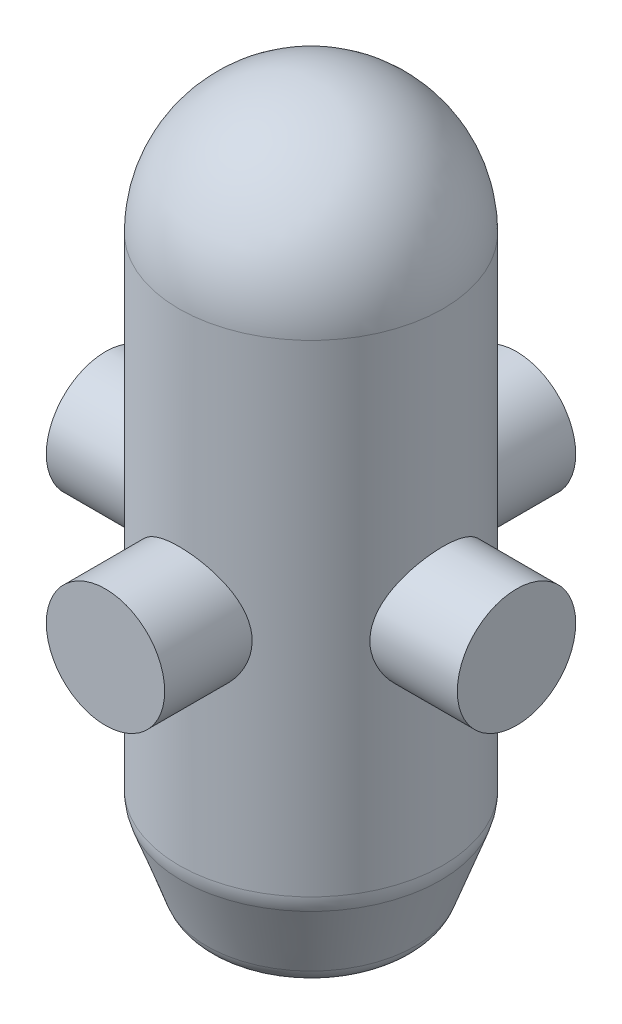
SolidWorks part; units mm, degrees
material "Ceramic Porcelain"
ref_plane "Front" through (0, 0, 0) normal (0, 0, 1) x (1, 0, 0)
ref_plane "Top"
ref_plane "Right" through (0, 0, 0) normal (1, 0, 0) x (0, 0, -1)
sketch "Sketch1" plane through (0, 0, 0) normal (0, 0, 1) x (1, 0, 0)
  line L0 (0, 0) -> (6.2866, 0)
  line L1 (6.2866, 0) -> (6.2866, -23.3)
  line L2 (6.2866, -23.3) -> (4.6488, -27.8)
  line L3 (4.6488, -27.8) -> (0, -27.8)
  line L4 (0, -27.8) -> (0, 0)
  dimension "D1" = 6.2866
  dimension "D2" = 27.8
  dimension "D3" = 20
  dimension "D4" = 4.5
revolve "Revolve1" add sketch "Sketch1" angle 360 about L4
fillet "Fillet1" radius 2 1 edges at (0, -23.3, -6.2866)
fillet "Fillet2" radius 1.3 1 edges at (0, -27.8, -4.6488)
sketch "Sketch2" plane through (0, 0, 0) normal (1, 0, 0) x (0, 0, -1)
  circle A0 centre (0, -12.615) radius 2.817
  dimension "D1" = 5.6341
  dimension "D2" = 12.615
extrude "Boss-Extrude1" add sketch "Sketch2" along normal mid plane 19.57
move or copy body "Body-Move/Copy1" bodies to move or copy 102 copy yes number of copies 1 rotation origin (0, 0, 0) rotation axis (0, 1, 0) rotation angle 90
sketch "Sketch3" plane through (0, 0, 0) normal (0, 0, 1) x (1, 0, 0)
  line L0 (6.2866, 0) -> (-6.2866, 0) construction
  line L1 (-6.2866, 0) -> (0, 0)
  line L2 (0, 0) -> (0, 6.2866)
  arc A0 (0, 6.2866) -> (-6.2866, 0) centre (0, 0) ccw
revolve "Revolve2" add sketch "Sketch3" angle 360 about L2
scale "Scale1" scale about centroid uniform scaling yes scale factor 10
